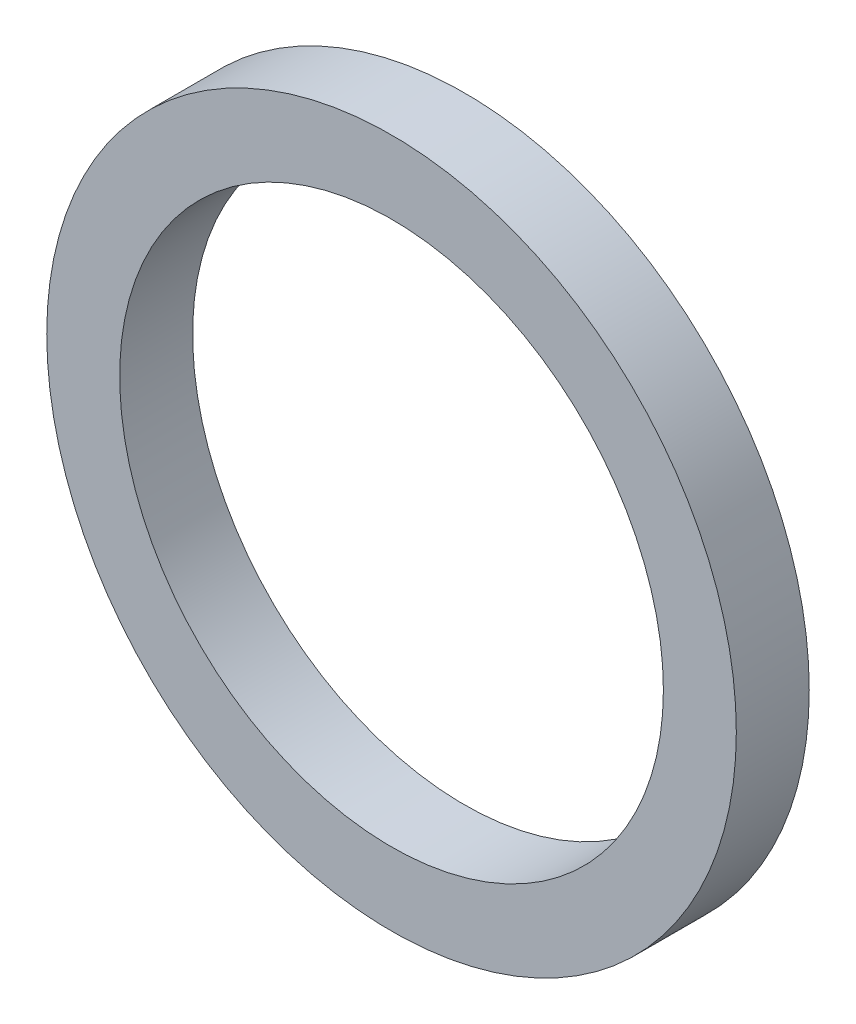
SolidWorks part; units mm, degrees
ref_plane "Front Plane" through (0, 0, 0) normal (0, 0, 1) x (1, 0, 0)
ref_plane "Top Plane" through (0, 0, 0) normal (0, 1, 0) x (1, 0, 0)
ref_plane "Right Plane" through (0, 0, 0) normal (1, 0, 0) x (0, 0, -1)
sketch "Sketch1" plane through (0, 0, 0) normal (0, 0, 1) x (1, 0, 0)
  circle A0 centre (0, 0) radius 4.1
  circle A1 centre (0, 0) radius 5.2
extrude "Boss-Extrude1" add sketch "Sketch1" along normal blind 1.1
